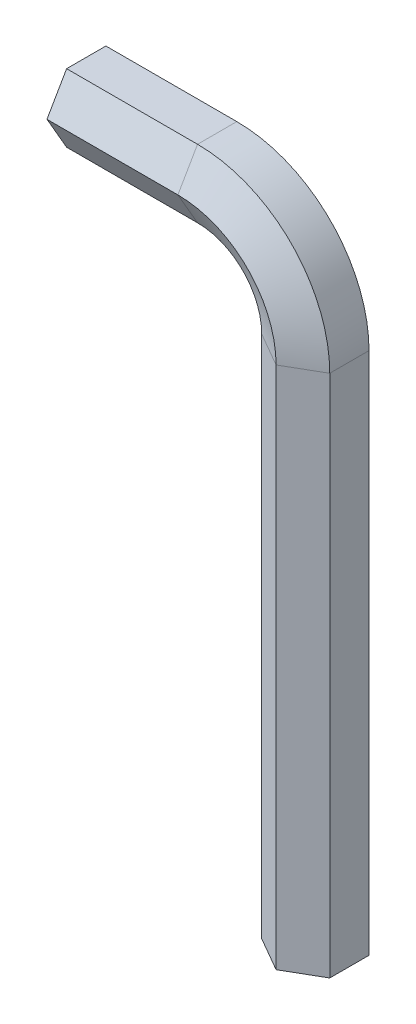
SolidWorks part; units mm, degrees
ref_plane "Front Plane" through (0, 0, 0) normal (0, 0, 1) x (1, 0, 0)
ref_plane "Top Plane" through (0, 0, 0) normal (0, 1, 0) x (1, 0, 0)
ref_plane "Right Plane" through (0, 0, 0) normal (1, 0, 0) x (0, 0, -1)
sketch "Sketch1" plane through (0, 0, 0) normal (0, 0, 1) x (1, 0, 0)
  line L0 (0, 0) -> (0, 80)
  line L1 (-15, 95) -> (-35, 95)
  arc A0 (0, 80) -> (-15, 95) centre (-15, 80) ccw
  dimension "D3" = 15
  dimension "D1" = 80
  dimension "D2" = 20
  dimension "D4" = 15
  dimension "D5" = 15
ref_plane "Plane1" through (-35, 95, 0) normal (-1, 0, 0) x (0, 0, 1)
sketch "Sketch2" plane through (-35, 95, 0) normal (-1, 0, 0) x (0, 0, 1)
  line L0 (0, -15) -> (0, 0) construction
  line L1 (6, 0) -> (3, 5.1962)
  line L2 (3, 5.1962) -> (-3, 5.1962)
  line L3 (-3, 5.1962) -> (-6, 0)
  line L4 (-6, 0) -> (-3, -5.1962)
  line L5 (-3, -5.1962) -> (3, -5.1962)
  line L6 (3, -5.1962) -> (6, 0)
  circle A0 centre (0, 0) radius 5.1962 construction
  dimension "D1" = 6
sweep "Sweep1" add profiles "Sketch2" path "Sketch1"
